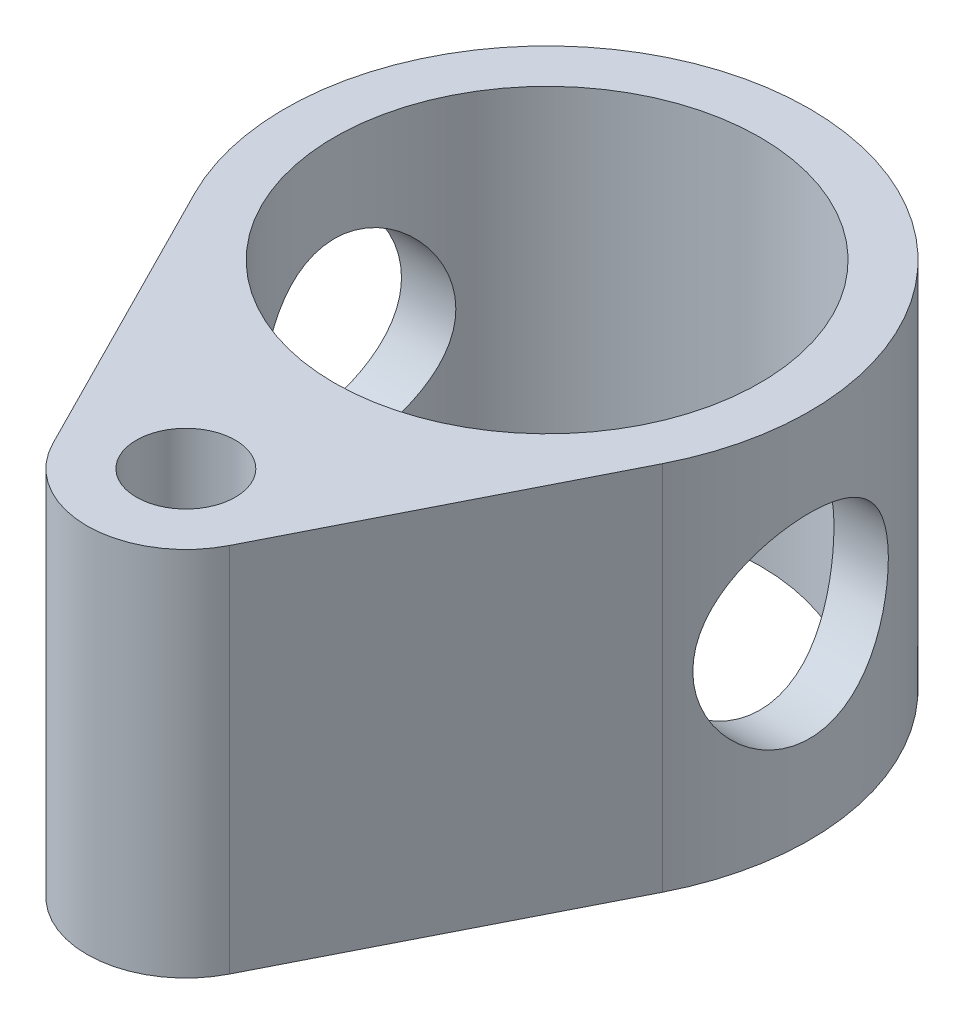
SolidWorks part; units mm, degrees
ref_plane "Front Plane" through (0, 0, 0) normal (0, 0, 1) x (1, 0, 0)
ref_plane "Top Plane" through (0, 0, 0) normal (0, 1, 0) x (1, 0, 0)
ref_plane "Right Plane" through (0, 0, 0) normal (1, 0, 0) x (0, 0, -1)
sketch "Sketch1" plane through (0, 0, 0) normal (0, 1, 0) x (1, 0, 0)
  line L0 (-12.008, -6.0856) -> (-4.5313, -20.8384)
  line L1 (4.5313, -20.8384) -> (12.008, -6.0856)
  circle A0 centre (0, 0) radius 10.922
  arc A1 (12.008, -6.0856) -> (-12.008, -6.0856) centre (0, 0) ccw
  circle A2 centre (0, -18.542) radius 2.54
  arc A3 (-4.5313, -20.8384) -> (4.5313, -20.8384) centre (0, -18.542) ccw
  circle A4 centre (0, 0) radius 13.462 construction
  circle A5 centre (0, -18.542) radius 5.08 construction
  dimension "D1" = 21.844
  dimension "D3" = 5.08
  dimension "D2" = 2.54
  dimension "D4" = 2.54
extrude "Boss-Extrude1" add sketch "Sketch1" along normal blind 12.7
sketch "Sketch2" plane through (0, 0, 0) normal (0, -1, 0) x (1, 0, 0)
  line L2 (12.008, 6.0856) -> (4.5313, 20.8384)
  line L3 (-4.5313, 20.8384) -> (-12.008, 6.0856)
  line L4 (12.008, 6.0856) -> (4.5313, 20.8384)
  line L5 (-4.5313, 20.8384) -> (-12.008, 6.0856)
  arc A2 (-12.008, 6.0856) -> (12.008, 6.0856) centre (0, 0) ccw
  arc A3 (4.5313, 20.8384) -> (-4.5313, 20.8384) centre (0, 18.542) ccw
  arc A4 (-12.008, 6.0856) -> (12.008, 6.0856) centre (0, 0) ccw
  arc A5 (4.5313, 20.8384) -> (-4.5313, 20.8384) centre (0, 18.542) ccw
  arc M5 (-12.008, 6.0856) -> (12.008, 6.0856) centre (0, 0) ccw
  line M6 (12.008, 6.0856) -> (4.5313, 20.8384)
  arc M7 (4.5313, 20.8384) -> (-4.5313, 20.8384) centre (0, 18.542) ccw
  line M8 (-4.5313, 20.8384) -> (-12.008, 6.0856)
  circle M9 centre (0, 0) radius 10.922
  circle M10 centre (0, 18.542) radius 2.54
  dimension "D1" = 0
extrude "Boss-Extrude2" add sketch "Sketch2" along normal blind 6.35 contours M8 M5 M6 M7 M9 M10 | M10
ref_plane "Plane1" through (13.462, 0, 0) normal (1, 0, 0) x (0, 0, -1)
sketch "Sketch3" plane through (13.462, 0, 0) normal (1, 0, 0) x (0, 0, -1)
  line L0 (13.462, 12.7) -> (-6.0856, 12.7) construction
  line L1 (10.922, 12.7) -> (-10.922, 12.7) construction
  line L2 (10.922, 12.7) -> (-10.922, 12.7)
  circle A0 centre (0, 3.175) radius 5.0165
  point P6 (0, 12.7)
  dimension "D2" = 10.033
  dimension "D1" = 9.525
extrude "Cut-Extrude1" cut sketch "Sketch3" against normal through all contours A0
